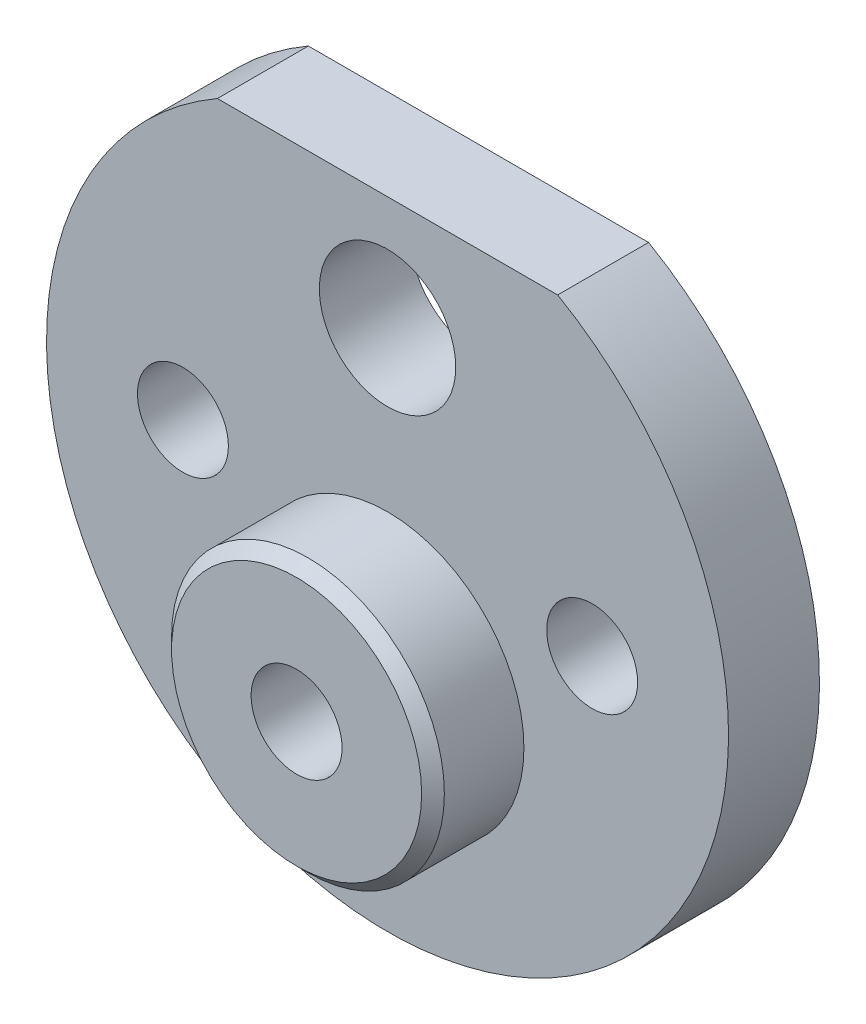
SolidWorks part; units mm, degrees
ref_plane "Front Plane" through (0, 0, 0) normal (0, 0, 1) x (1, 0, 0)
ref_plane "Top Plane" through (0, 0, 0) normal (0, 1, 0) x (1, 0, 0)
ref_plane "Right Plane" through (0, 0, 0) normal (1, 0, 0) x (0, 0, -1)
sketch "Sketch2" plane through (0, 0, 0) normal (0, 0, 1) x (1, 0, 0)
  line L0 (-7.4833, 13) -> (7.4833, 13)
  arc A0 (-7.4833, 13) -> (7.4833, 13) centre (0, 0) ccw
  circle A1 centre (0, 8) radius 3
  circle A2 centre (9, 0) radius 2
  circle A3 centre (-9, 0) radius 2
  point P10 (0, 0)
  point P11 (0, 0)
  point P12 (0, 0)
  point P13 (0, 0)
  dimension "D1" = 30
  dimension "D6" = 6
  dimension "D7" = 4
  dimension "D8" = 4
  dimension "D2" = 13
  dimension "D3" = 8
  dimension "D4" = 9
  dimension "D5" = 9
extrude "Boss-Extrude1" add sketch "Sketch2" along normal blind 4
sketch "Sketch3" plane through (0, 0, 4) normal (0, 0, 1) x (1, 0, 0)
  circle A0 centre (0, -5) radius 6
  point P2 (0, 0)
  dimension "D2" = 12
  dimension "D1" = 5
extrude "Boss-Extrude2" add sketch "Sketch3" along normal blind 4
chamfer "Chamfer1" distance 0.5 angle 45 1 edges at (6, -5, 8)
sketch "Sketch4" plane through (0, 0, 8) normal (0, 0, 1) x (1, 0, 0)
  circle A0 centre (0, -5) radius 2
  dimension "D1" = 4
extrude "Cut-Extrude1" cut sketch "Sketch4" against normal through all
